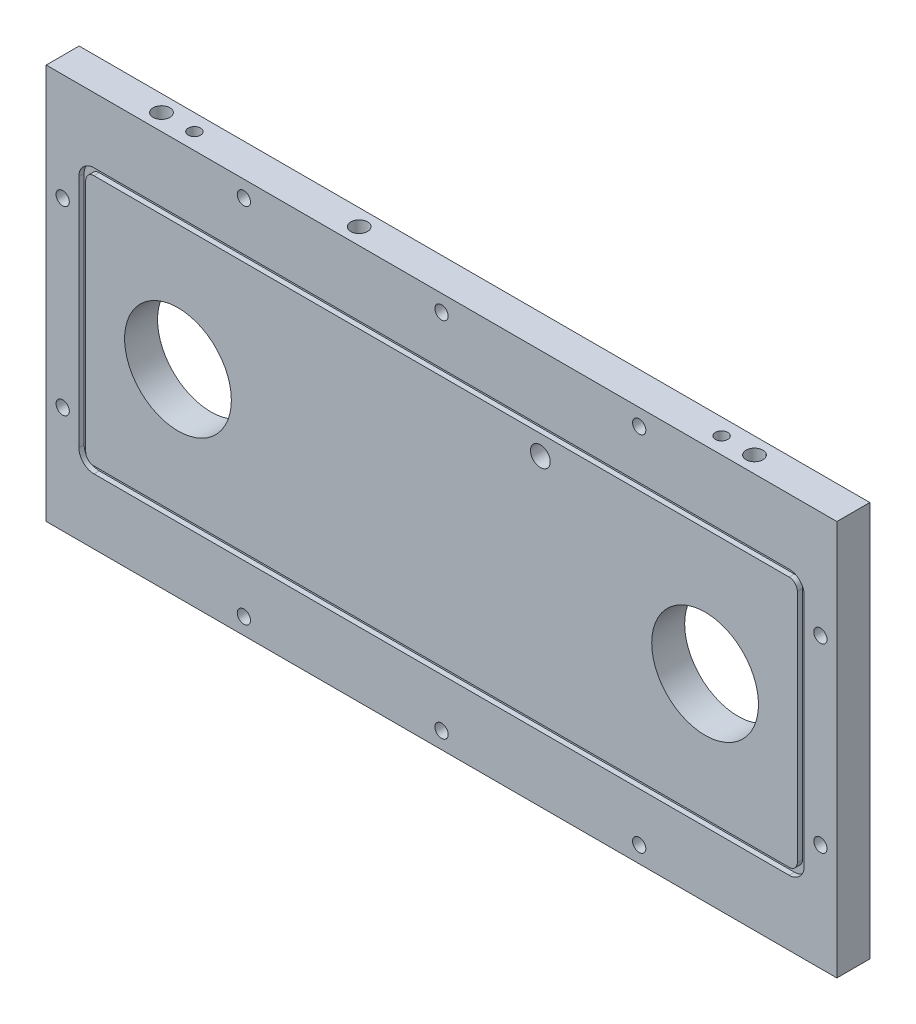
SolidWorks part; units mm, degrees
ref_plane "Front Plane" through (0, 0, 0) normal (0, 0, 1) x (1, 0, 0)
ref_plane "Top Plane" through (0, 0, 0) normal (0, 1, 0) x (1, 0, 0)
ref_plane "Right Plane" through (0, 0, 0) normal (1, 0, 0) x (0, 0, -1)
ref_plane "Plane1" through (0, 0, 12.7) normal (0, 0, 1) x (1, 0, 0)
sketch "Sketch1" plane through (0, 0, 12.7) normal (0, 0, 1) x (1, 0, 0)
  line L0 (152.4, -76.2) -> (152.4, 76.2)
  line L1 (152.4, 76.2) -> (-152.4, 76.2)
  line L2 (-152.4, 76.2) -> (-152.4, -76.2)
  line L3 (-152.4, -76.2) -> (152.4, -76.2)
  dimension "D1" = 152.4
  dimension "D2" = 304.8
  dimension "D3" = 152.4
  dimension "D4" = 76.2
extrude "Boss-Extrude1" add sketch "Sketch1" against normal blind 12.7
sketch "Sketch2" plane through (0, 0, 12.7) normal (0, 0, 1) x (1, 0, 0)
  line L0 (-139.8016, -51.0921) -> (139.8016, -51.0921)
  line L1 (139.8016, -51.0921) -> (139.8016, 51.0921)
  line L2 (139.8016, 51.0921) -> (-139.8016, 51.0921)
  line L3 (-139.8016, 51.0921) -> (-139.8016, -51.0921)
extrude "Cut-Extrude1" cut sketch "Sketch2" against normal blind 2.032
sketch "Sketch3" plane through (0, 0, 10.668) normal (0, 0, 1) x (1, 0, 0)
  line L0 (137.16, 48.4505) -> (137.16, -48.4505)
  line L1 (137.16, -48.4505) -> (-137.16, -48.4505)
  line L2 (-137.16, -48.4505) -> (-137.16, 48.4505)
  line L3 (-137.16, 48.4505) -> (137.16, 48.4505)
extrude "Boss-Extrude2" add sketch "Sketch3" along normal blind 2.032
hole_wizard "M36 Clearance Hole1" positions "Sketch5" profile "Sketch4" hole size "M36" standard "ANSI Metric"
sketch "Sketch5" plane through (0, 0, 0) normal (0, 0, -1) x (-1, 0, 0)
  point P0 (-101.6, 0)
sketch "Sketch4" plane through (101.6, 0, 0) normal (1, 0, 0) x (0, 1, 0)
  line L0 (0, 0) -> (0, 12.7)
  line L1 (0, 12.7) -> (20.574, 12.7)
  line L2 (20.574, 12.7) -> (20.574, 0)
  line L5 (20.574, 0) -> (0, 0)
  line L11 (0, -6.35) -> (0, 107.95) construction
  dimension "Thru Hole Dia." = 41.148
  dimension "Thru Hole Depth" = 12.7
hole_wizard "M7 Clearance Hole1" positions "Sketch7" profile "Sketch6" hole size "M7" standard "ANSI Metric" end condition through all
sketch "Sketch7" plane through (0, 0, 0) normal (0, 0, -1) x (-1, 0, 0)
  line L0 (-152.4, 76.2) -> (152.4, 76.2) construction
  line L1 (-152.4, -76.2) -> (-152.4, 76.2) construction
  point P0 (-38.1, 40.8686)
  dimension "D1" = 35.3314
  dimension "D2" = 114.3
sketch "Sketch6" plane through (38.1, 40.8686, 0) normal (1, 0, 0) x (0, 1, 0)
  line L0 (0, 0) -> (0, 12.7)
  line L1 (0, 12.7) -> (3.81, 12.7)
  line L2 (3.81, 12.7) -> (3.81, 0)
  line L5 (3.81, 0) -> (0, 0)
  line L11 (0, -6.35) -> (0, 107.95) construction
  dimension "Thru Hole Dia." = 7.62
  dimension "Thru Hole Depth" = 12.7
hole_wizard "M36 Clearance Hole2" positions "Sketch11" profile "Sketch10" hole size "M36" standard "ANSI Metric"
sketch "Sketch11" plane through (0, 0, 12.7) normal (0, 0, 1) x (1, 0, 0)
  point P0 (-101.6, 0)
sketch "Sketch10" plane through (-101.6, 0, 12.7) normal (1, 0, 0) x (0, -1, 0)
  line L0 (0, 0) -> (0, 12.7)
  line L1 (0, 12.7) -> (20.574, 12.7)
  line L2 (20.574, 12.7) -> (20.574, 0)
  line L5 (20.574, 0) -> (0, 0)
  line L11 (0, -6.35) -> (0, 107.95) construction
  dimension "Thru Hole Dia." = 41.148
  dimension "Thru Hole Depth" = 12.7
hole_wizard "M3.5 Clearance Hole2" positions "Sketch13" profile "Sketch12" hole size "M3.5" standard "ANSI Metric"
sketch "Sketch13" plane through (0, 0, 0) normal (0, 0, -1) x (-1, 0, 0)
  point P0 (-74.7636, -15.494)
  point P1 (-101.6, -30.988)
  point P2 (-101.6, 30.988)
  point P3 (-128.4364, 15.494)
  point P4 (-128.4364, -15.494)
  point P5 (-74.7636, 15.494)
  point P6 (101.6, 30.988)
  point P7 (128.4364, 15.494)
  point P8 (128.4364, -15.494)
  point P9 (101.6, -30.988)
  point P10 (74.7636, -15.494)
  point P11 (74.7636, 15.494)
sketch "Sketch12" plane through (74.7636, -15.494, 0) normal (1, 0, 0) x (0, 1, 0)
  line L0 (0, 0) -> (0, 9.0148)
  line L1 (0, 9.0148) -> (1.8986, 7.874)
  line L2 (1.8986, 7.874) -> (1.8986, 0)
  line L5 (1.8986, 0) -> (0, 0)
  line L10 (0, 9.0148) -> (-1.8986, 7.874) construction
  line L11 (0, -6.35) -> (0, 107.95) construction
  dimension "Hole Dia." = 3.7973
  dimension "Hole Depth" = 7.874
  dimension "Drill Angle" = 118
hole_wizard "CBORE for #10 Binding Head Machine Screw1" positions "Sketch15" profile "Sketch14" counterbore size "#10" standard "ANSI Inch" end condition through all
sketch "Sketch15" plane through (0, 0, 0) normal (0, 0, -1) x (-1, 0, 0)
  line L0 (-152.4, 76.2) -> (152.4, 76.2) construction
  line L1 (-152.4, -76.2) -> (-152.4, 76.2) construction
  point P1 (0, 69.85)
  point P2 (-76.2, 69.85)
  point P3 (-146.05, 34.925)
  point P13 (0, 76.2)
  dimension "D1" = 6.35
  dimension "D2" = 6.35
  dimension "D3" = 6.35
  dimension "D4" = 76.2
  dimension "D5" = 41.275
sketch "Sketch14" plane through (0, 69.85, 0) normal (1, 0, 0) x (0, 1, 0)
  line L0 (0, 0) -> (0, 12.7)
  line L1 (0, 12.7) -> (2.5527, 12.7)
  line L3 (2.5527, 12.7) -> (2.5527, 3.1242)
  line L4 (2.5527, 3.1242) -> (5.5562, 3.1242)
  line L5 (5.5562, 3.1242) -> (5.5562, 0)
  line L7 (5.5562, 0) -> (0, 0)
  line L11 (0, -6.35) -> (0, 107.95) construction
  dimension "Thru Hole Dia." = 5.1054
  dimension "Thru Hole Depth" = 12.7
  dimension "C'Bore Dia." = 11.1125
  dimension "C'Bore Depth" = 3.1242
hole_wizard "M4 Clearance Hole1" positions "Sketch17" profile "Sketch16" hole size "M4" standard "ANSI Metric"
sketch "Sketch17" plane through (0, 76.2, 0) normal (0, 1, 0) x (1, 0, 0)
  point P0 (101.6, -6.35)
  point P1 (-101.6, -6.35)
sketch "Sketch16" plane through (101.6, 76.2, 6.35) normal (1, 0, 0) x (0, 0, 1)
  line L0 (0, 0) -> (0, 14.1308)
  line L1 (0, 14.1308) -> (2.3812, 12.7)
  line L2 (2.3812, 12.7) -> (2.3812, 0)
  line L5 (2.3812, 0) -> (0, 0)
  line L10 (0, 14.1308) -> (-2.3812, 12.7) construction
  line L11 (0, -6.35) -> (0, 107.95) construction
  dimension "Hole Dia." = 4.7625
  dimension "Hole Depth" = 12.7
  dimension "Drill Angle" = 118
hole_wizard "M4 Clearance Hole2" positions "Sketch19" profile "Sketch18" hole size "M4" standard "ANSI Metric"
sketch "Sketch19" plane through (0, -76.2, 0) normal (0, -1, 0) x (-1, 0, 0)
  point P0 (101.6, -6.35)
  point P1 (-101.6, -6.35)
sketch "Sketch18" plane through (-101.6, -76.2, 6.35) normal (1, 0, 0) x (0, 0, -1)
  line L0 (0, 0) -> (0, 14.1308)
  line L1 (0, 14.1308) -> (2.3812, 12.7)
  line L2 (2.3812, 12.7) -> (2.3812, 0)
  line L5 (2.3812, 0) -> (0, 0)
  line L10 (0, 14.1308) -> (-2.3812, 12.7) construction
  line L11 (0, -6.35) -> (0, 107.95) construction
  dimension "Hole Dia." = 4.7625
  dimension "Hole Depth" = 12.7
  dimension "Drill Angle" = 118
fillet "Fillet1" radius 3.175 4 edges at (137.16, -48.4505, 11.684) (137.16, 48.4505, 11.684) (-137.16, -48.4505, 11.684) (-137.16, 48.4505, 11.684)
fillet "Fillet2" radius 5.8166 4 edges at (-139.8016, 51.0921, 11.684) (-139.8016, -51.0921, 11.684) (139.8016, 51.0921, 11.684) (139.8016, -51.0921, 11.684)
mirror "Mirror1" about plane through (0, 0, 0) normal (1, 0, 0) of "CBORE for #10 Binding Head Machine Screw1"
mirror "Mirror2" about plane through (0, 0, 0) normal (0, 1, 0) of "Mirror1", "CBORE for #10 Binding Head Machine Screw1"
hole_wizard "#10-24 Tapped Hole1" positions "Sketch21" profile "Sketch20" tap size "#10-24" standard "ANSI Inch"
sketch "Sketch21" plane through (0, 0, 0) normal (0, 0, -1) x (-1, 0, 0)
  point P0 (-38.1, 59.8686)
  dimension "D1" = 19
sketch "Sketch20" plane through (38.1, 59.8686, 0) normal (1, 0, 0) x (0, 1, 0)
  line L0 (0, 0) -> (0, 8.8904)
  line L1 (0, 8.8904) -> (1.8986, 7.7495)
  line L2 (1.8986, 7.7495) -> (1.8986, 0)
  line L5 (1.8986, 0) -> (0, 0)
  line L10 (0, 8.8904) -> (-1.8987, 7.7495) construction
  line L11 (0, -6.35) -> (0, 107.95) construction
  dimension "Tap Drill Dia." = 3.7973
  dimension "Tap Drill Depth" = 7.7495
  dimension "Drill Angle" = 118
pattern_circular "CirPattern1" count 6 over 360 about axis through (38.1, 40.8686, 0) along (0, 0, 1) of "#10-24 Tapped Hole1"
sketch "Sketch22" plane through (0, 76.2, 0) normal (0, 1, 0) x (1, 0, 0)
  line L1 (152.4, 0) -> (-152.4, 0) construction
  line L2 (-152.4, 0) -> (-152.4, -12.7) construction
  circle A1 centre (-38.1, -6.35) radius 3.2385
  point P0 (-152.4, -6.35)
  dimension "D4" = 6.477
  dimension "D1" = 114.3
  dimension "D2" = 6.35
extrude "Cut-Extrude2" cut sketch "Sketch22" against normal blind 76.2
sketch "Sketch23" plane through (0, 76.2, 0) normal (0, 1, 0) x (1, 0, 0)
  line L0 (152.4, 0) -> (-152.4, 0) construction
  line L3 (-152.4, 0) -> (-152.4, -12.7) construction
  circle A1 centre (-114.3, -6.35) radius 3.2385
  dimension "D4" = 6.477
  dimension "D2" = 38.1
  dimension "D1" = 6.35
extrude "Cut-Extrude3" cut sketch "Sketch23" against normal blind 50.8
mirror "Mirror5" about plane through (0, 0, 0) normal (0, 1, 0) of "Cut-Extrude3"
mirror "Mirror6" about plane through (0, 0, 0) normal (1, 0, 0) of "Mirror5", "Cut-Extrude3"
sketch "Sketch24" plane through (0, -76.2, 0) normal (0, -1, 0) x (1, 0, 0)
  line L0 (-152.4, 0) -> (152.4, 0) construction
  line L1 (152.4, 0) -> (152.4, 12.7) construction
  circle A0 centre (38.1, 6.35) radius 3.2385
  point P4 (152.4, 6.35)
  dimension "D1" = 6.477
  dimension "D2" = 6.35
  dimension "D3" = 114.3
extrude "Cut-Extrude4" cut sketch "Sketch24" against normal blind 76.2
equation "\"D3@Sketch1\"=\"D2@Sketch1\"/2"
equation "\"D4@Sketch1\"=\"D1@Sketch1\"/2"
